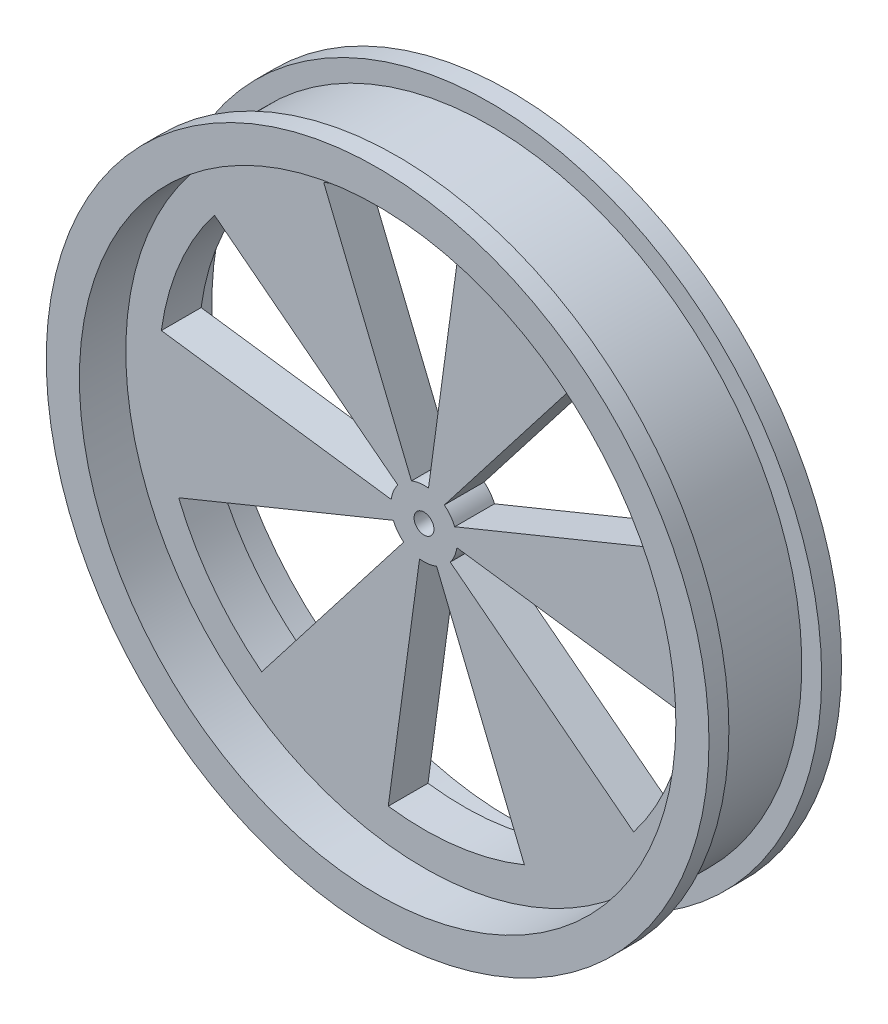
SolidWorks part; units mm, degrees
material "PVC rigide"
ref_plane "Plan de face" through (0, 0, 0) normal (0, 0, 1) x (1, 0, 0)
ref_plane "Plan de dessus" through (0, 0, 0) normal (0, 1, 0) x (1, 0, 0)
ref_plane "Plan de droite" through (0, 0, 0) normal (1, 0, 0) x (0, 0, -1)
sketch "Esquisse2" plane through (0, 0, 0) normal (0, 0, 1) x (1, 0, 0)
  circle A0 centre (0, 0) radius 50
  dimension "D1" = 100
extrude "Boss.-Extru.1" add sketch "Esquisse2" along normal blind 20
sketch "Esquisse3" plane through (0, 0, 0) normal (0, 0, 1) x (1, 0, 0)
  circle A0 centre (0, 0) radius 45
  dimension "D1" = 90
extrude "Enlèv. mat.-Extru.1" cut sketch "Esquisse3" along normal blind 7
sketch "Esquisse4" plane through (0, 0, 20) normal (0, 0, 1) x (1, 0, 0)
  circle A0 centre (0, 0) radius 45
  dimension "D1" = 90
extrude "Enlèv. mat.-Extru.2" cut sketch "Esquisse4" against normal blind 7
sketch "Esquisse6" plane through (0, 0, 13) normal (0, 0, 1) x (1, 0, 0)
  line L0 (4.6279, 1.8928) -> (37.0231, 15.1423)
  line L1 (4.9543, -0.6747) -> (39.6341, -5.3979)
  line L3 (3.9531, -3.0615) -> (31.6252, -24.4918)
  line L4 (1.8928, -4.6279) -> (15.1423, -37.0231)
  line L5 (-0.6747, -4.9543) -> (-5.3979, -39.6341)
  line L6 (-3.0615, -3.9531) -> (-24.4918, -31.6252)
  line L7 (-4.6279, -1.8928) -> (-37.0231, -15.1423)
  line L8 (-4.9543, 0.6747) -> (-39.6341, 5.3979)
  line L9 (-3.9531, 3.0615) -> (-31.6252, 24.4918)
  line L10 (-1.8928, 4.6279) -> (-15.1423, 37.0231)
  line L11 (0.6747, 4.9543) -> (5.3979, 39.6341)
  line L12 (3.0615, 3.9531) -> (24.4918, 31.6252)
  circle A0 centre (0, 0) radius 40
  circle A1 centre (0, 0) radius 5
  point P32 (0, 0)
  dimension "D1" = 80
  dimension "D2" = 10
  dimension "D3" = 12
extrude "Enlèv. mat.-Extru.3" cut sketch "Esquisse6" against normal through all contours A1 L0 A0 L12 | A1 L11 A0 L10 | A1 L9 A0 L8 | A1 L7 A0 L6 | A1 L5 A0 L4 | A1 L3 A0 L1
sketch "Esquisse7" plane through (0, 0, 0) normal (1, 0, 0) x (0, 0, -1)
  line L1 (-17, 51.1265) -> (-3, 51.1265)
  line L2 (-17, 51.1265) -> (-17, 47)
  line L3 (-17, 47) -> (-3, 47)
  line L4 (-3, 51.1265) -> (-3, 47)
  line L5 (0, 0) -> (-30.1089, 0)
  point P7 (0, 0)
  dimension "D1" = 47
  dimension "D2" = 14
  dimension "D3" = 3
revolve "Enlèvement de matière-Révolution1" cut sketch "Esquisse7" angle 360 about L5
sketch "Esquisse8" plane through (0, 0, 0) normal (0, 0, 1) x (1, 0, 0)
  circle A0 centre (0, 0) radius 1.5
  dimension "D1" = 3
extrude "Enlèv. mat.-Extru.4" cut sketch "Esquisse8" along normal through all
